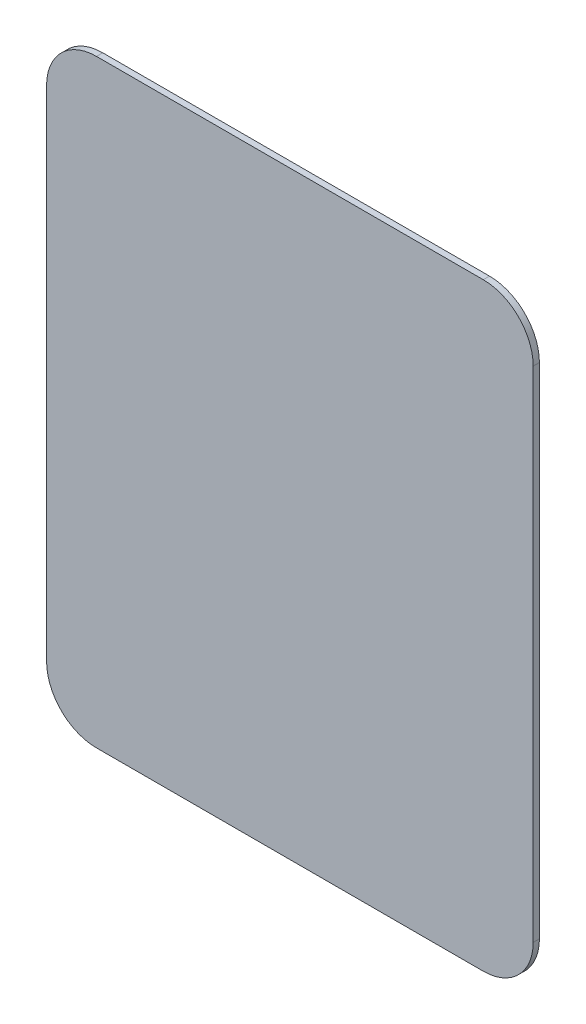
SolidWorks part; units mm, degrees
material "Bambu ABA Aero Approx."
ref_plane "Front Plane" through (0, 0, 0) normal (0, 0, 1) x (1, 0, 0)
ref_plane "Top Plane" through (0, 0, 0) normal (0, 1, 0) x (1, 0, 0)
ref_plane "Right Plane" through (0, 0, 0) normal (1, 0, 0) x (0, 0, -1)
sketch "Sketch2" plane through (0, 0, 0) normal (0, 0, 1) x (1, 0, 0)
  line L1 (-98.425, -152.4) -> (98.425, -152.4)
  line L2 (-123.825, -127) -> (-123.825, 127)
  line L3 (-98.425, 152.4) -> (98.425, 152.4)
  line L4 (123.825, -127) -> (123.825, 127)
  line L5 (-123.825, -152.4) -> (123.825, 152.4) construction
  line L6 (-123.825, 152.4) -> (123.825, -152.4) construction
  arc A0 (-98.425, -152.4) -> (-123.825, -127) centre (-98.425, -127) cw
  arc A1 (98.425, -152.4) -> (123.825, -127) centre (98.425, -127) ccw
  arc A2 (98.425, 152.4) -> (123.825, 127) centre (98.425, 127) cw
  arc A3 (-123.825, 127) -> (-98.425, 152.4) centre (-98.425, 127) cw
  point P0 (0, 0)
  dimension "D3" = 25.4
  dimension "D1" = 247.65
  dimension "D2" = 304.8
extrude "Boss-Extrude1" add sketch "Sketch2" along normal blind 3.175
